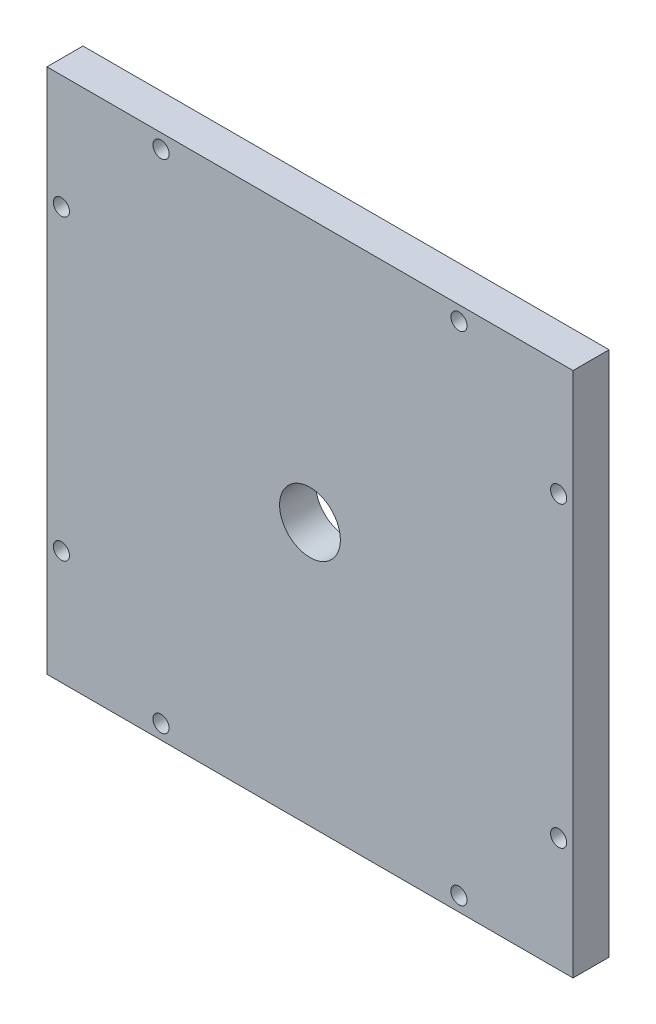
SolidWorks part; units mm, degrees
ref_plane "Front Plane" through (0, 0, 0) normal (0, 0, 1) x (1, 0, 0)
ref_plane "Top Plane" through (0, 0, 0) normal (0, 1, 0) x (1, 0, 0)
ref_plane "Right Plane" through (0, 0, 0) normal (1, 0, 0) x (0, 0, -1)
sketch "Sketch1" plane through (0, 0, 0) normal (0, 0, 1) x (1, 0, 0)
  line L0 (46.355, 92.71) -> (46.355, 0) construction
  line L1 (0, 0) -> (92.71, 0)
  line L2 (0, 0) -> (0, 92.71)
  line L3 (0, 92.71) -> (92.71, 92.71)
  line L4 (92.71, 0) -> (92.71, 92.71)
  line L5 (0, 46.355) -> (92.71, 46.355) construction
  circle A0 centre (46.355, 46.355) radius 5.3578
  dimension "D1" = 92.71
  dimension "D2" = 92.71
extrude "Boss-Extrude1" add sketch "Sketch1" along normal blind 6.35
sketch "Sketch2" plane through (0, 0, 6.35) normal (0, 0, 1) x (1, 0, 0)
  line L0 (46.355, 92.71) -> (46.355, 0) construction
  line L1 (92.71, 92.71) -> (0, 92.71) construction
  line L2 (0, 0) -> (92.71, 0) construction
  line L3 (0, 46.355) -> (92.71, 46.355) construction
  line L4 (0, 92.71) -> (0, 0) construction
  line L5 (92.71, 0) -> (92.71, 92.71) construction
  line L6 (0, 0) -> (92.71, 92.71) construction
  circle A0 centre (2.54, 20.1) radius 1.4224
  circle A1 centre (20.1, 2.54) radius 1.4224
  circle A2 centre (72.61, 2.54) radius 1.4224
  circle A3 centre (90.17, 20.1) radius 1.4224
  circle A4 centre (90.17, 72.61) radius 1.4224
  circle A5 centre (72.61, 90.17) radius 1.4224
  circle A6 centre (20.1, 90.17) radius 1.4224
  circle A7 centre (2.54, 72.61) radius 1.4224
extrude "Cut-Extrude1" cut sketch "Sketch2" against normal blind 6.35
